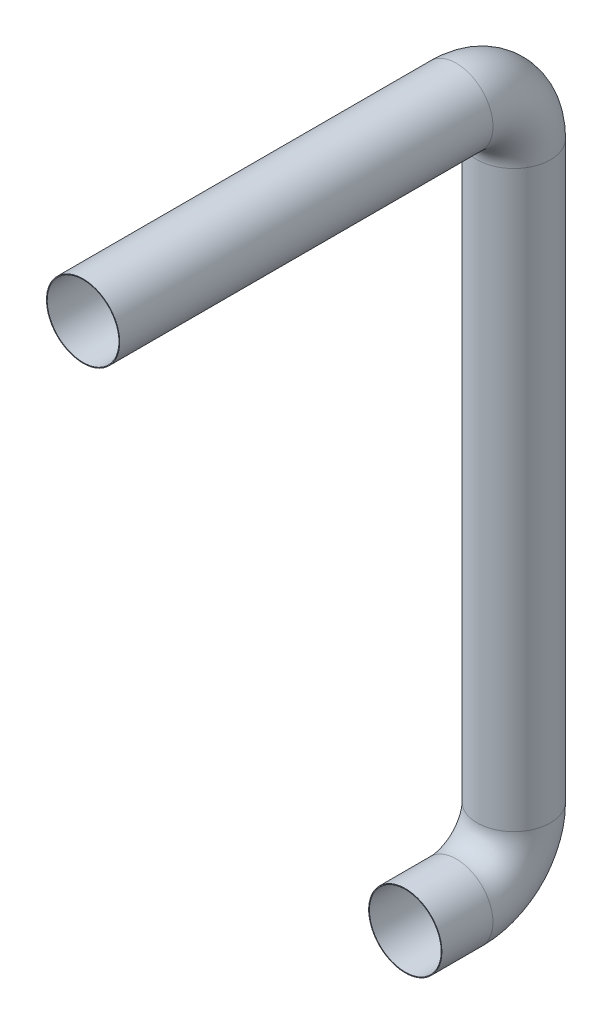
SolidWorks part; units mm, degrees
material "AISI 316 Stainless Steel Sheet (SS)"
ref_plane "Front Plane" through (0, 0, 0) normal (0, 0, 1) x (1, 0, 0)
ref_plane "Top Plane" through (0, 0, 0) normal (0, 1, 0) x (1, 0, 0)
ref_plane "Right Plane" through (0, 0, 0) normal (1, 0, 0) x (0, 0, -1)
sketch "Sketch31" plane through (0, 0, 0) normal (0, 0, 1) x (1, 0, 0)
  circle A0 centre (0, 0) radius 25
  circle A1 centre (0, 0) radius 25.5
  dimension "D1" = 50
  dimension "D2" = 0.5
sketch "Sketch3" plane through (0, 0, 0) normal (1, 0, 0) x (0, 0, -1)
  line L0 (0, 0) -> (260, 0)
  line L1 (300, -40) -> (300, -440)
  line L2 (260, -480) -> (224.43, -480)
  arc A0 (260, 0) -> (300, -40) centre (260, -40) cw
  arc A1 (300, -440) -> (260, -480) centre (260, -440) cw
  dimension "D1" = 300
  dimension "D3" = 40
  dimension "D2" = 400
  dimension "D4" = 35.57
sweep "Sweep1" add profiles "Sketch31" path "Sketch3"
